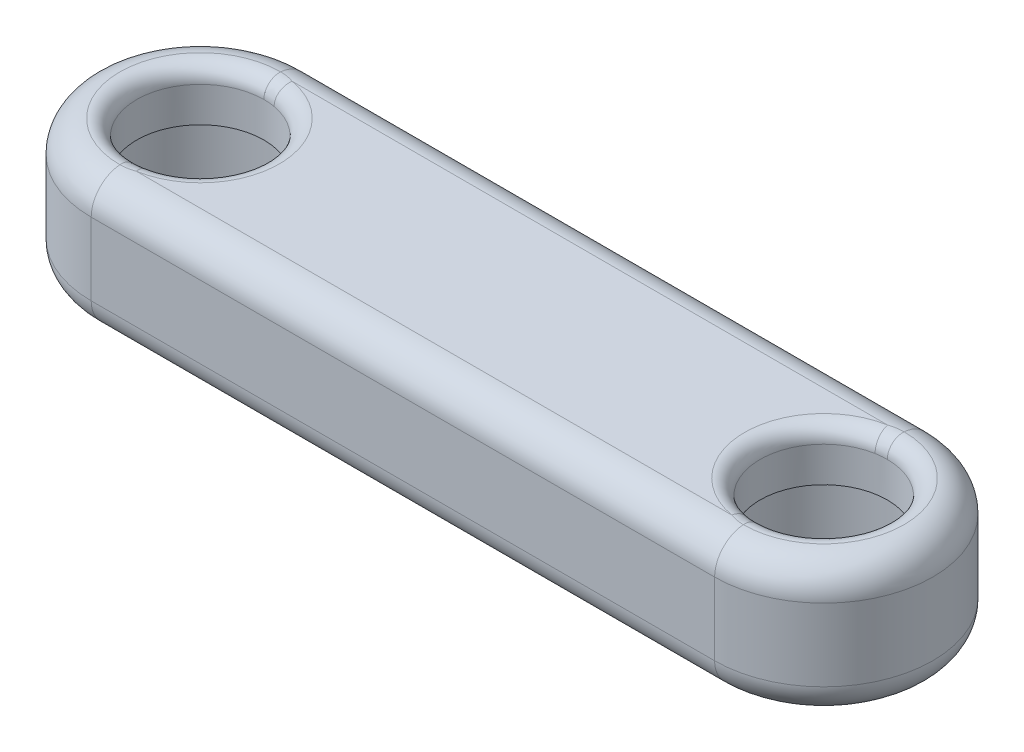
SolidWorks part; units mm, degrees
material "1060 Alloy"
ref_plane "Front Plane" through (0, 0, 0) normal (0, 0, 1) x (1, 0, 0)
ref_plane "Top Plane" through (0, 0, 0) normal (0, 1, 0) x (1, 0, 0)
ref_plane "Right Plane" through (0, 0, 0) normal (1, 0, 0) x (0, 0, -1)
sketch "Sketch1" plane through (0, 0, 0) normal (0, 1, 0) x (1, 0, 0)
  line L0 (-20, 0) -> (20, 0) construction
  line L1 (-20, 7) -> (20, 7)
  line L2 (-20, -7) -> (20, -7)
  arc A0 (-20, 7) -> (-20, -7) centre (-20, 0) ccw
  arc A1 (20, -7) -> (20, 7) centre (20, 0) ccw
  circle A2 centre (-20, 0) radius 4.08
  circle A3 centre (20, 0) radius 4.08
  point P3 (0, 0)
  dimension "D1" = 8.16
  dimension "D2" = 8.16
  dimension "D4" = 7
  dimension "D3" = 40
extrude "Boss-Extrude1" add sketch "Sketch1" along normal blind 8.65
sketch "Sketch2" plane through (0, 0, 0) normal (0, -1, 0) x (1, 0, 0)
  circle A0 centre (-20, 0) radius 5.08
  circle A1 centre (20, 0) radius 5.08
  dimension "D1" = 10.16
  dimension "D2" = 10.16
extrude "Cut-Extrude1" cut sketch "Sketch2" against normal blind 4.4 from offset 1 offset against normal yes
fillet "Fillet1" radius 2 8 edges at (0, 8.65, -7) (27, 8.65, 0) (0, 8.65, 7) (0, 0, -7) (27, 0, 0) (0, 0, 7) (-27, 8.65, 0) (-27, 0, 0)
fillet "Fillet2" radius 1 2 edges at (-20, 8.65, 4.08) (20, 8.65, 4.08)
